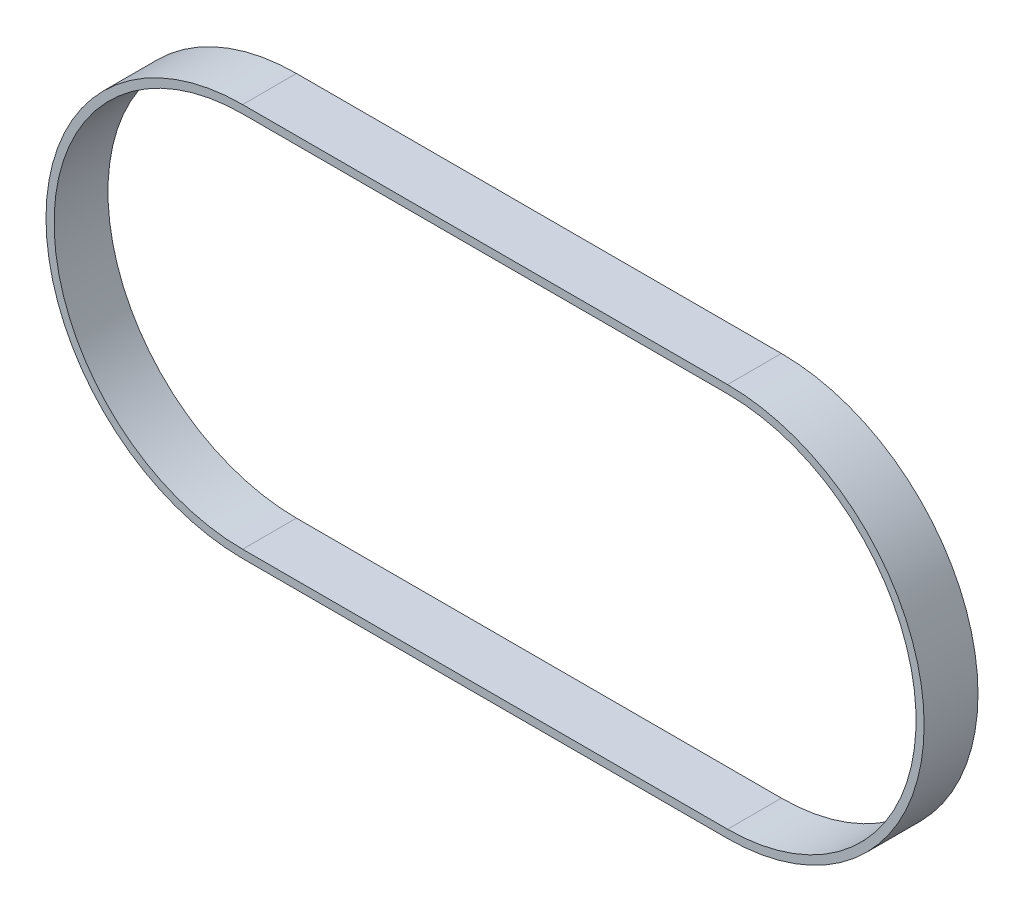
SolidWorks part; units mm, degrees
material "HYPALON"
ref_plane "Front Plane" through (0, 0, 0) normal (0, 0, 1) x (1, 0, 0)
ref_plane "Top Plane" through (0, 0, 0) normal (0, 1, 0) x (1, 0, 0)
ref_plane "Right Plane" through (0, 0, 0) normal (1, 0, 0) x (0, 0, -1)
sketch "Sketch1" plane through (0, 0, 0) normal (0, 0, 1) x (1, 0, 0)
  line L0 (-53.685, -5.9466) -> (36.3592, -5.9466) construction
  line L1 (-53.685, 29.0534) -> (36.3592, 29.0534)
  line L2 (-53.685, -40.9466) -> (36.3592, -40.9466)
  line L3 (-53.685, 30.5534) -> (36.3592, 30.5534)
  line L4 (-53.685, -42.4466) -> (36.3592, -42.4466)
  arc A0 (-53.685, 29.0534) -> (-53.685, -40.9466) centre (-53.685, -5.9466) ccw
  arc A1 (36.3592, -40.9466) -> (36.3592, 29.0534) centre (36.3592, -5.9466) ccw
  arc A2 (36.3592, -42.4466) -> (36.3592, 30.5534) centre (36.3592, -5.9466) ccw
  arc A3 (-53.685, 30.5534) -> (-53.685, -42.4466) centre (-53.685, -5.9466) ccw
  point P2 (-8.6629, -5.9466)
  dimension "D1" = 35
  dimension "D2" = 400
  dimension "D3" = 90.0443
  dimension "D4" = 1.5
extrude "Boss-Extrude1" add sketch "Sketch1" along normal blind 10
